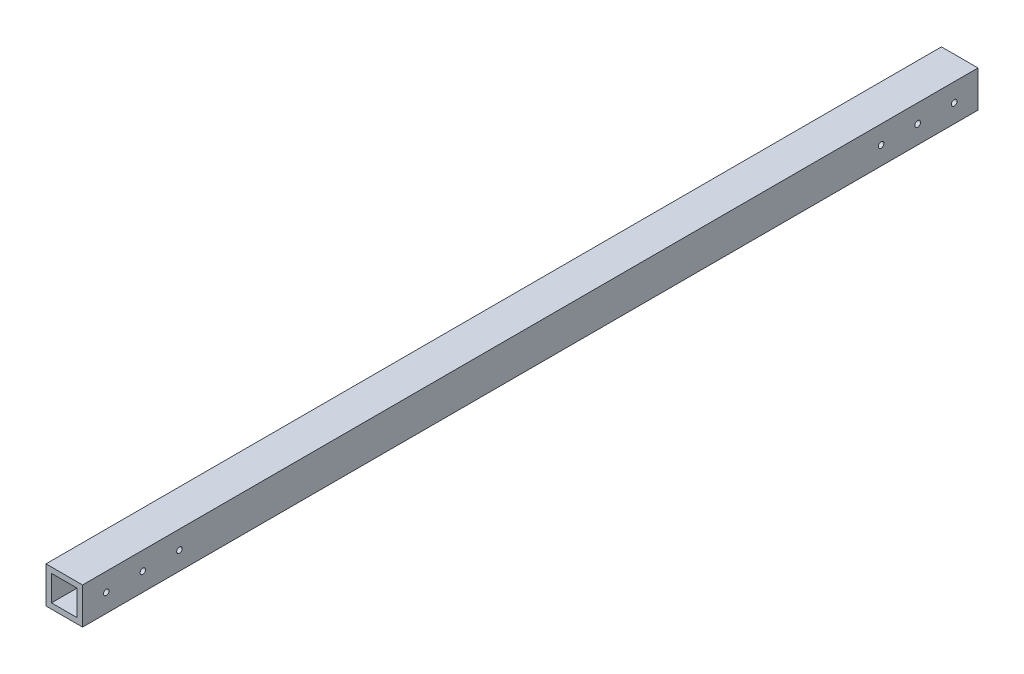
SolidWorks part; units mm, degrees
ref_plane "前视基准面" through (0, 0, 0) normal (0, 0, 1) x (1, 0, 0)
ref_plane "上视基准面" through (0, 0, 0) normal (0, 1, 0) x (1, 0, 0)
ref_plane "右视基准面" through (0, 0, 0) normal (1, 0, 0) x (0, 0, -1)
other "Configuration Table"
sketch "草图1" plane through (0, 0, 0) normal (0, 0, 1) x (1, 0, 0)
  line L0 (-9.3333, 11.0061) -> (-9.3333, -8.9939)
  line L1 (-9.3333, 11.0061) -> (10.6667, 11.0061)
  line L2 (-9.3333, -8.9939) -> (10.6667, -8.9939)
  line L3 (10.6667, 11.0061) -> (10.6667, -8.9939)
  dimension "D1" = 20
  dimension "D2" = 20
extrude "凸台-拉伸1" add sketch "草图1" along normal blind 490
sketch "草图2" plane through (0, 0, 0) normal (0, 0, -1) x (-1, 0, 0)
  line L0 (-10.6667, -8.9939) -> (-10.6667, 11.0061) construction
  line L1 (-7.6667, 8.0061) -> (6.3333, 8.0061)
  line L2 (-7.6667, 8.0061) -> (-7.6667, -5.9939)
  line L3 (-7.6667, -5.9939) -> (6.3333, -5.9939)
  line L4 (6.3333, 8.0061) -> (6.3333, -5.9939)
  line L5 (9.3333, 11.0061) -> (9.3333, -8.9939) construction
  line L6 (9.3333, -8.9939) -> (-10.6667, -8.9939) construction
  line L7 (-10.6667, 11.0061) -> (9.3333, 11.0061) construction
  dimension "D1" = 3
  dimension "D2" = 3
  dimension "D3" = 3
  dimension "D4" = 3
extrude "切除-拉伸1" cut sketch "草图2" against normal through all
sketch "草图3" plane through (10.6667, 0, 0) normal (1, 0, 0) x (0, 0, -1)
  circle A0 centre (-477, 1.0061) radius 1.5
  circle A1 centre (-457, 1.0061) radius 1.5
  circle A2 centre (-437, 1.0061) radius 1.5
extrude "切除-拉伸2" cut sketch "草图3" against normal blind 80
sketch "草图4" plane through (-9.3333, 0, 0) normal (-1, 0, 0) x (0, 0, 1)
  circle A0 centre (13, 1.0061) radius 1.55
  circle A1 centre (33, 1.0061) radius 1.55
  circle A2 centre (53, 1.0061) radius 1.55
extrude "切除-拉伸3" cut sketch "草图4" against normal blind 27
